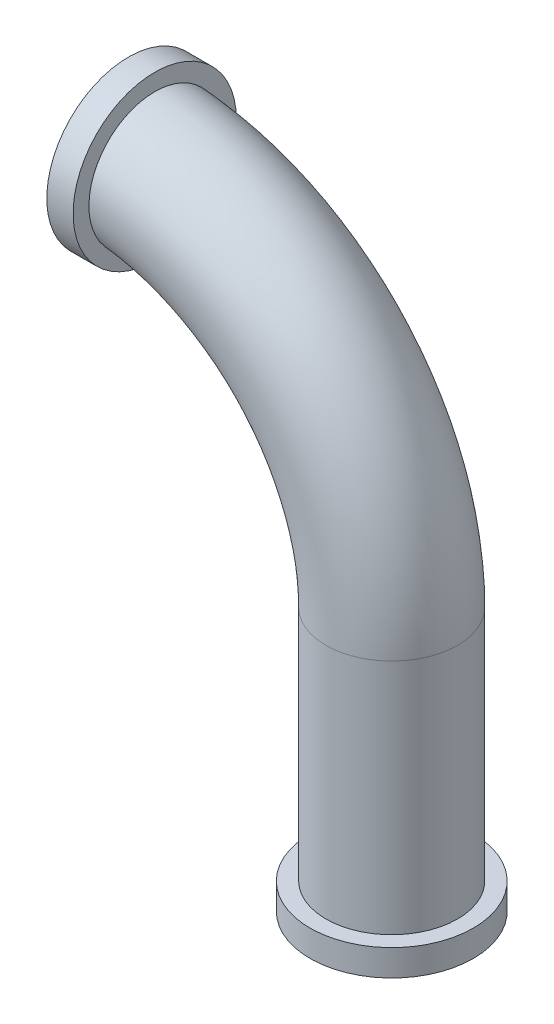
SolidWorks part; units mm, degrees
ref_plane "Ön Düzlem" through (0, 0, 0) normal (0, 0, 1) x (1, 0, 0)
ref_plane "Üst Düzlem" through (0, 0, 0) normal (0, 1, 0) x (1, 0, 0)
ref_plane "Sağ Düzlem" through (0, 0, 0) normal (1, 0, 0) x (0, 0, -1)
sketch "Çizim1" plane through (0, 0, 0) normal (0, 0, 1) x (1, 0, 0)
  line L0 (1, 0) -> (1, -1)
  arc A0 (0, 1) -> (1, 0) centre (0, 0) cw
sketch "Çizim3" plane through (0, 0, 0) normal (1, 0, 0) x (0, 0, -1)
  line L0 (0, 1) -> (0, 0) construction
  circle A0 centre (0, 1) radius 0.2
sketch "Çizim4" plane through (0, 0, 0) normal (1, 0, 0) x (0, 0, -1)
  circle A0 centre (0, 1) radius 0.21
sweep "Süpür-İnce1" add profiles "Çizim3" path "Çizim1" parameters "D1"=0.05
ref_plane "Düzlem1" through (0, -1, 0) normal (0, -1, 0) x (-1, 0, 0)
sketch "Çizim5" plane through (0, -1, 0) normal (0, -1, 0) x (-1, 0, 0)
  circle A0 centre (-1, 0) radius 0.21
sketch "Çizim6" plane through (0, 0, 0) normal (0, 0, 1) x (1, 0, 0)
  line L0 (1, -1) -> (1, -0.9)
  line L1 (0.79, -1) -> (1.21, -1) construction
sketch "Çizim7" plane through (0, 0, 0) normal (0, 0, 1) x (1, 0, 0)
  line L0 (0, 1) -> (0.1, 1)
  line L1 (0, 0.79) -> (0, 1.21) construction
sweep "Süpür-İnce2" add profiles "Çizim4" path "Çizim7" parameters "D1"=0.1
sweep "Süpür-İnce3" add profiles "Çizim5" path "Çizim6" parameters "D1"=0.1
